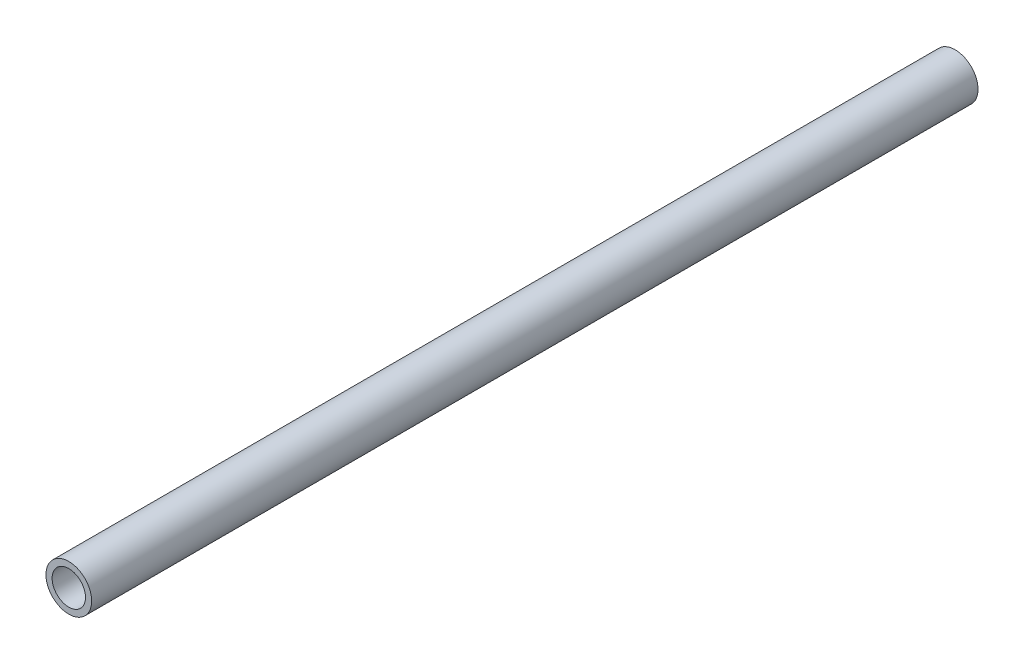
SolidWorks part; units mm, degrees
material "PVC Rígido"
ref_plane "Alzado" through (0, 0, 0) normal (0, 0, 1) x (1, 0, 0)
ref_plane "Planta" through (0, 0, 0) normal (0, 1, 0) x (1, 0, 0)
ref_plane "Vista lateral" through (0, 0, 0) normal (1, 0, 0) x (0, 0, -1)
sketch "Croquis1" plane through (0, 0, 0) normal (0, 0, 1) x (1, 0, 0)
  circle A0 centre (0, 0) radius 10.7
  circle A1 centre (0, 0) radius 7.825
  dimension "D1" = 21.4
  dimension "D2" = 15.65
extrude "Saliente-Extruir1" add sketch "Croquis1" along normal mid plane 415
